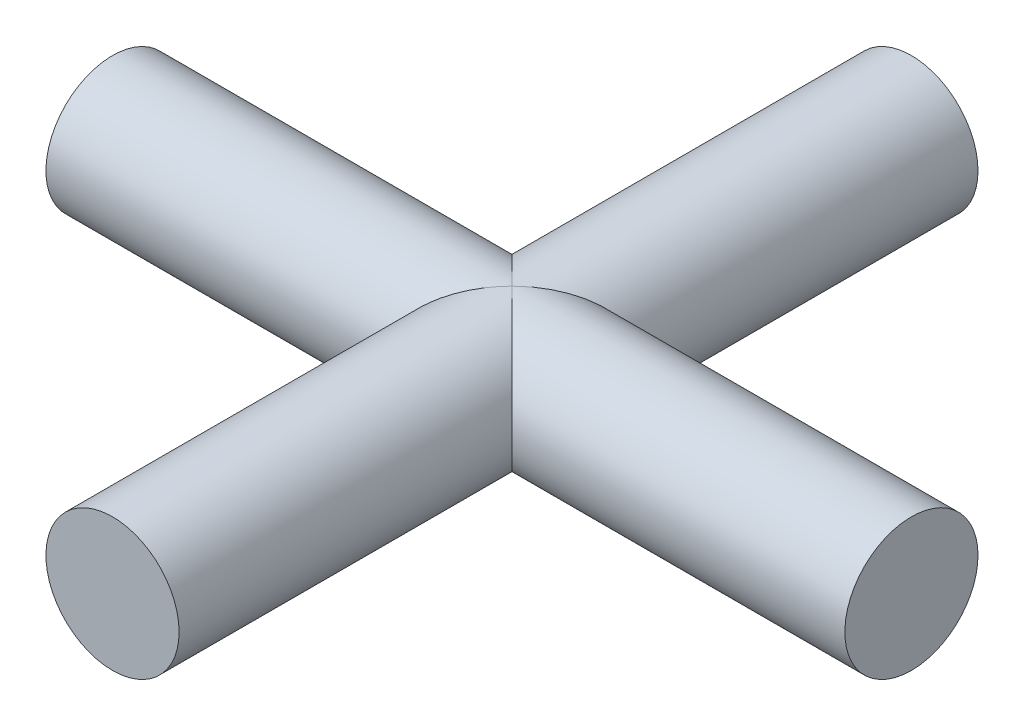
SolidWorks part; units mm, degrees
ref_plane "Plan de face" through (0, 0, 0) normal (0, 0, 1) x (1, 0, 0)
ref_plane "Plan de dessus" through (0, 0, 0) normal (0, 1, 0) x (1, 0, 0)
ref_plane "Plan de droite" through (0, 0, 0) normal (1, 0, 0) x (0, 0, -1)
sketch "Esquisse1" plane through (0, 0, 0) normal (0, 0, 1) x (1, 0, 0)
  circle A0 centre (0, 0) radius 2.5
  dimension "D1" = 5
extrude "Boss.-Extru.1" add sketch "Esquisse1" along normal mid plane 30 contours A0
sketch "Esquisse3" plane through (0, 0, 0) normal (1, 0, 0) x (0, 0, -1)
  circle A0 centre (0, 0) radius 2.5
  dimension "D1" = 5
extrude "Boss.-Extru.2" add sketch "Esquisse3" along normal mid plane 30
